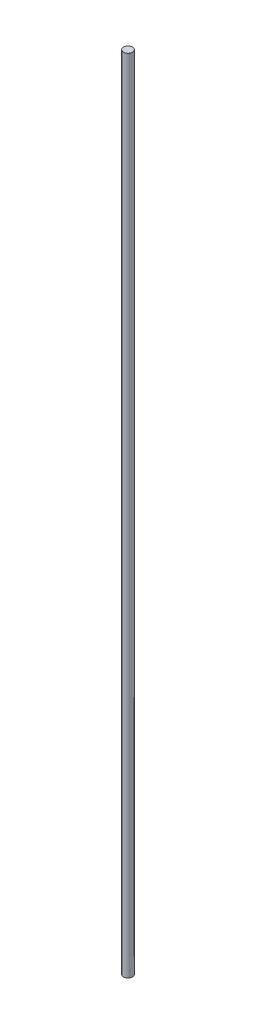
SolidWorks part; units mm, degrees
material "Glass"
ref_plane "Front Plane" through (0, 0, 0) normal (0, 0, 1) x (1, 0, 0)
ref_plane "Top Plane" through (0, 0, 0) normal (0, 1, 0) x (1, 0, 0)
ref_plane "Right Plane" through (0, 0, 0) normal (1, 0, 0) x (0, 0, -1)
sketch "Sketch1" plane through (0, 0, 0) normal (0, 1, 0) x (1, 0, 0)
  circle A0 centre (0, 0) radius 0.2125
  dimension "D1" = 0.425
extrude "Boss-Extrude1" add sketch "Sketch1" along normal blind 38.1
